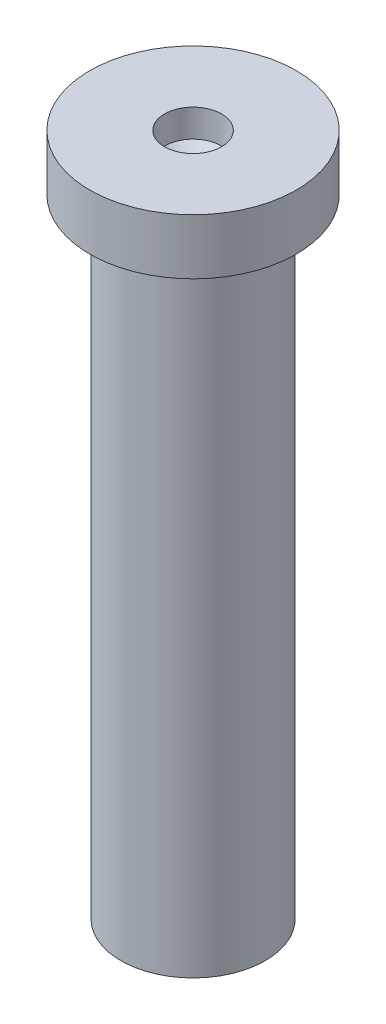
SolidWorks part; units mm, degrees
ref_plane "Front Plane" through (0, 0, 0) normal (0, 0, 1) x (1, 0, 0)
ref_plane "Top Plane" through (0, 0, 0) normal (0, 1, 0) x (1, 0, 0)
ref_plane "Right Plane" through (0, 0, 0) normal (1, 0, 0) x (0, 0, -1)
sketch "Sketch1" plane through (0, 0, 0) normal (0, 0, 1) x (1, 0, 0)
  line L0 (0, 0) -> (0, 14.575) construction
  line L1 (0, 0) -> (1.3, 0)
  line L2 (1.3, 0) -> (1.3, 11.3)
  line L3 (1.3, 11.3) -> (1.8614, 11.3)
  line L4 (1.8614, 11.3) -> (1.8614, 12.3)
  line L5 (1.8614, 12.3) -> (0.5132, 12.3)
  line L6 (0.5132, 12.3) -> (0.5132, 11.8)
  line L7 (0, 0) -> (0, 11.4402)
  line L8 (0.5132, 11.8) -> (0, 11.4402)
  dimension "D1" = 2.6
  dimension "D2" = 11.3
  dimension "D3" = 1
revolve "Revolve1" add sketch "Sketch1" angle 360 about L0
